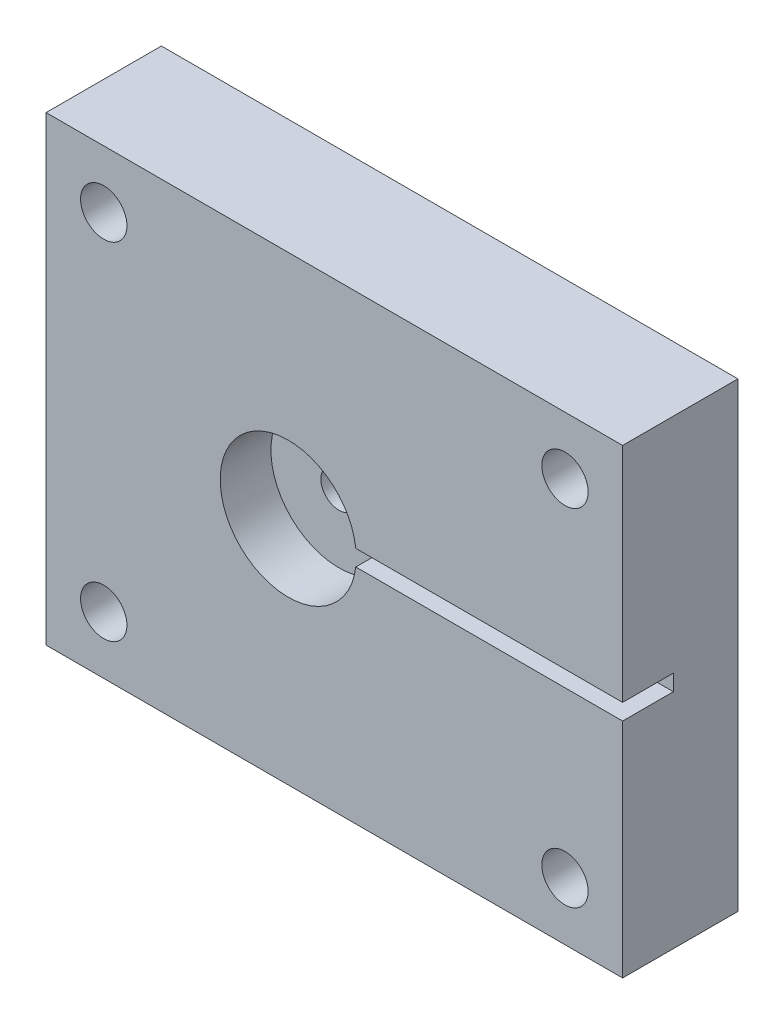
SolidWorks part; units mm, degrees
ref_plane "Front Plane" through (0, 0, 0) normal (0, 0, 1) x (1, 0, 0)
ref_plane "Top Plane" through (0, 0, 0) normal (0, 1, 0) x (1, 0, 0)
ref_plane "Right Plane" through (0, 0, 0) normal (1, 0, 0) x (0, 0, -1)
sketch "Sketch1" plane through (0, 0, 0) normal (0, 0, 1) x (1, 0, 0)
  line L1 (-31.75, 25.4) -> (31.75, 25.4)
  line L2 (-31.75, 25.4) -> (-31.75, -25.4)
  line L3 (-31.75, -25.4) -> (31.75, -25.4)
  line L4 (31.75, 25.4) -> (31.75, -25.4)
  line L5 (-31.75, 25.4) -> (31.75, -25.4) construction
  line L6 (-31.75, -25.4) -> (31.75, 25.4) construction
  point P0 (0, 0)
  dimension "D1" = 63.5
  dimension "D2" = 50.8
extrude "Boss-Extrude1" add sketch "Sketch1" along normal blind 12.7
ref_plane "Plane2" through (0, 0, 4.572) normal (0, 0, -1) x (-1, 0, 0)
ref_plane "Plane3" through (0, 0, 7.112) normal (0, 0, -1) x (-1, 0, 0)
sketch "Sketch2" plane through (0, 0, 12.7) normal (0, 0, 1) x (1, 0, 0)
  circle A0 centre (-5.08, 0) radius 7.493
  point P8 (0, 0)
  dimension "D1" = 14.986
  dimension "D2" = 5.08
extrude "Cut-Extrude1" cut sketch "Sketch2" against normal up to surface (5.588 mm away)
sketch "Sketch3" plane through (0, 0, 12.7) normal (0, 0, 1) x (1, 0, 0)
  line L0 (31.75, -25.4) -> (31.75, 25.4) construction
  line L1 (0, 0.889) -> (31.75, 0.889)
  line L2 (0, 0.889) -> (0, -0.889)
  line L3 (0, -0.889) -> (31.75, -0.889)
  line L4 (31.75, 0.889) -> (31.75, -0.889)
  point P6 (0, 0)
  dimension "D1" = 1.778
extrude "Cut-Extrude2" cut sketch "Sketch3" against normal up to surface (5.588 mm away)
sketch "Sketch9" plane through (0, 0, 7.112) normal (0, 0, 1) x (1, 0, 0)
  circle A0 centre (-5.08, 0) radius 1.9939
  point P5 (0, 0)
  dimension "D1" = 3.9878
  dimension "D2" = 5.08
extrude "Cut-Extrude3" cut sketch "Sketch9" against normal blind 11.9888
sketch "Sketch10" plane through (0, 0, 0) normal (0, 0, -1) x (-1, 0, 0)
  circle A1 centre (5.08, 0) radius 7.493
  circle A2 centre (5.08, 0) radius 7.493
  dimension "D1" = 0
extrude "Cut-Extrude4" cut sketch "Sketch10" against normal up to surface (4.572 mm away)
sketch "Sketch11" plane through (0, 0, 12.7) normal (0, 0, 1) x (1, 0, 0)
  line L1 (-25.4, 19.05) -> (25.4, 19.05) construction
  line L2 (-25.4, 19.05) -> (-25.4, -19.05) construction
  line L3 (-25.4, -19.05) -> (25.4, -19.05) construction
  line L4 (25.4, 19.05) -> (25.4, -19.05) construction
  line L5 (-25.4, 19.05) -> (25.4, -19.05) construction
  line L6 (-25.4, -19.05) -> (25.4, 19.05) construction
  circle A0 centre (-25.4, 19.05) radius 2.5527
  point P0 (0, 0)
  point P8 (0, 0)
  dimension "D3" = 5.1054
  dimension "D1" = 50.8
  dimension "D2" = 38.1
extrude "Cut-Extrude5" cut sketch "Sketch11" against normal through all
mirror "Mirror1" about plane through (0, 0, 0) normal (1, 0, 0) of "Cut-Extrude5"
mirror "Mirror2" about plane through (0, 0, 0) normal (0, 1, 0) of "Mirror1", "Cut-Extrude5"
